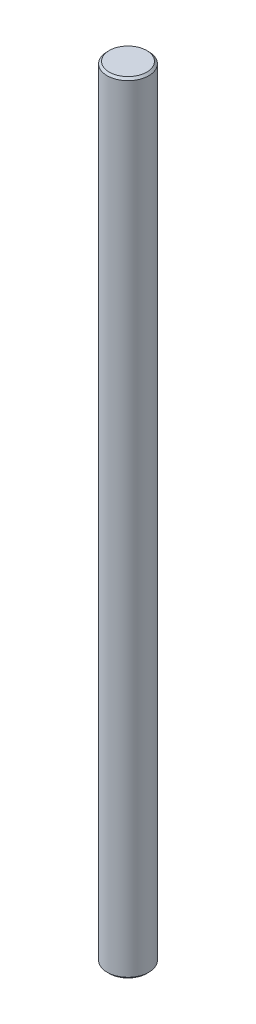
SolidWorks part; units mm, degrees
ref_plane "Front Plane" through (0, 0, 0) normal (0, 0, 1) x (1, 0, 0)
ref_plane "Top Plane" through (0, 0, 0) normal (0, 1, 0) x (1, 0, 0)
ref_plane "Right Plane" through (0, 0, 0) normal (1, 0, 0) x (0, 0, -1)
sketch "Sketch1" plane through (0, 0, 0) normal (0, 1, 0) x (1, 0, 0)
  circle A0 centre (0, 0) radius 2
  dimension "D1" = 4
extrude "Boss-Extrude1" add sketch "Sketch1" along normal mid plane 75
chamfer "Chamfer1" distance 0.2 angle 45 2 edges at (0, -37.5, 2) (0, 37.5, 2)
